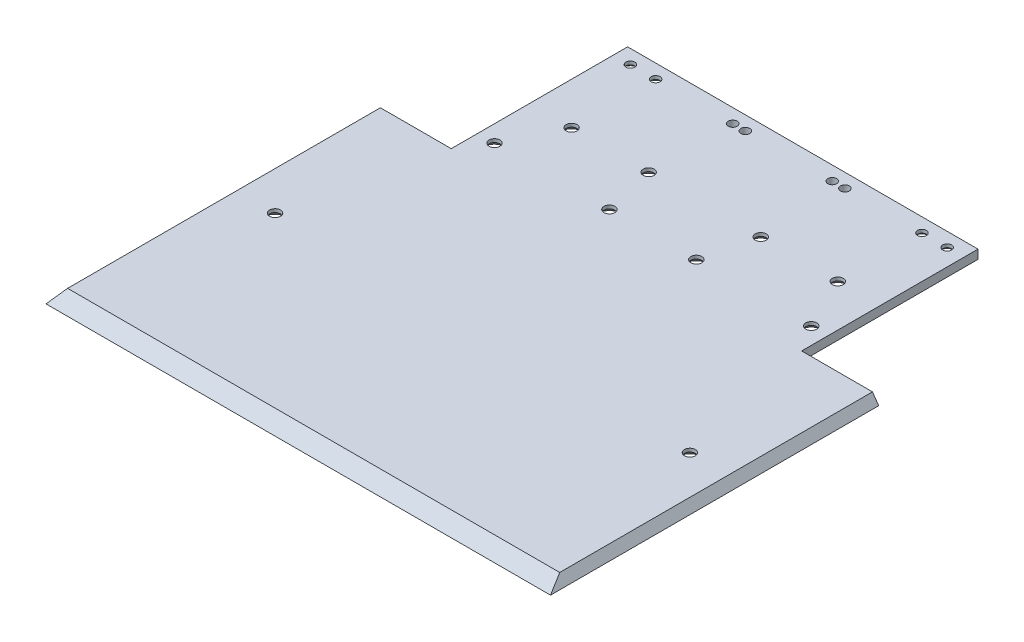
SolidWorks part; units mm, degrees
ref_plane "Alzado" through (0, 0, 0) normal (0, 0, 1) x (1, 0, 0)
ref_plane "Planta" through (0, 0, 0) normal (0, 1, 0) x (1, 0, 0)
ref_plane "Vista lateral" through (0, 0, 0) normal (1, 0, 0) x (0, 0, -1)
sketch "Croquis1" plane through (0, 0, 0) normal (0, 1, 0) x (1, 0, 0)
  line L0 (-62.5, 90) -> (-62.5, 27.08)
  line L1 (90, -90) -> (-90, -90)
  line L2 (90, -90) -> (90, 27.08)
  line L3 (62.5, 90) -> (-62.5, 90)
  line L4 (-90, -90) -> (-90, 27.08)
  line L5 (90, -90) -> (-62.5, 62.5) construction
  line L6 (62.5, 62.5) -> (-90, -90) construction
  line L7 (-62.5, 27.08) -> (-90, 27.08)
  line L8 (0, 90) -> (0, -90) construction
  line L9 (62.5, 27.08) -> (90, 27.08)
  line L10 (62.5, 90) -> (62.5, 27.08)
  point P0 (0, 0)
  dimension "D1" = 125
  dimension "D2" = 180
  dimension "D3" = 27.5
  dimension "D4" = 62.92
  dimension "D5" = 27.5
extrude "Saliente-Extruir1" add sketch "Croquis1" along normal blind 3.17
sketch "Croquis2" plane through (-90, 0, 0) normal (-1, 0, 0) x (0, 0, 1)
  line L0 (90, 0) -> (84.5094, 3.17)
  line L1 (-27.08, 3.17) -> (90, 3.17) construction
  line L2 (84.5094, 3.17) -> (90, 3.17)
  line L3 (90, 3.17) -> (90, 0)
  dimension "D1" = 60
extrude "Cortar-Extruir1" cut sketch "Croquis2" against normal up to next
sketch "Croquis16" plane through (0, 0, -27.08) normal (0, 0, -1) x (-1, 0, 0)
  line L0 (90, 3.17) -> (90, 0)
  line L1 (90, 0) -> (87.7803, 3.17)
  line L2 (62.5, 3.17) -> (90, 3.17) construction
  line L3 (87.7803, 3.17) -> (90, 3.17)
  dimension "D1" = 35
extrude "Cortar-Extruir7" cut sketch "Croquis16" against normal up to next
mirror "Simetría4" about plane through (0, 0, 0) normal (1, 0, 0) of "Cortar-Extruir7"
sketch "Croquis3" plane through (0, 3.17, 0) normal (0, 1, 0) x (1, 0, 0)
  circle A0 centre (74, -24.2793) radius 1.585
extrude "Cortar-Extruir2" cut sketch "Croquis3" against normal up to next (3.17 mm away)
mirror "Simetría1" about plane through (0, 0, 0) normal (1, 0, 0) of "Cortar-Extruir2"
sketch "Croquis4" plane through (0, 3.17, 0) normal (0, 1, 0) x (1, 0, 0)
  circle A0 centre (-56.5, 36.5006) radius 1.585
  circle A1 centre (-15.5, 36.5006) radius 1.585
  circle A2 centre (-15.5, 85.0006) radius 1.585
  circle A3 centre (-56.5, 85.0006) radius 1.585
extrude "Cortar-Extruir3" cut sketch "Croquis4" against normal up to next
sketch "Croquis6" plane through (0, 3.17, 0) normal (0, 1, 0) x (1, 0, 0)
  circle A0 centre (56.5, 85.0006) radius 1.585
  circle A1 centre (15.5, 85.0006) radius 1.585
  circle A2 centre (15.5, 36.5006) radius 1.585
  circle A3 centre (56.5, 36.5006) radius 1.585
extrude "Cortar-Extruir4" cut sketch "Croquis6" against normal up to next
sketch "Croquis7" plane through (0, 3.17, 0) normal (0, 1, 0) x (1, 0, 0)
  circle A0 centre (-20, 85.0006) radius 1.585
  circle A1 centre (-47.5, 85.0006) radius 1.585
  circle A2 centre (-47.5, 55.0006) radius 1.585
  circle A3 centre (-20, 55.0006) radius 1.585
extrude "Cortar-Extruir5" cut sketch "Croquis7" against normal up to next (3.17 mm away)
mirror "Simetría2" about plane through (0, 0, 0) normal (1, 0, 0) of "Cortar-Extruir5"
sketch "Croquis15" plane through (0, 0, 0) normal (0, -1, 0) x (-1, 0, 0)
  circle A0 centre (20, 55.0006) radius 4
  circle A1 centre (15.5, 36.5006) radius 4
  circle A2 centre (56.5, 36.5006) radius 4
  circle A3 centre (47.5, 55.0006) radius 4
  circle A4 centre (56.5, 85.0006) radius 4
  circle A5 centre (47.5, 85.0006) radius 4
  circle A8 centre (74, -24.2793) radius 4
  dimension "D1" = 8
  dimension "D3" = 8
  dimension "D4" = 8
  dimension "D5" = 8
  dimension "D6" = 8
  dimension "D7" = 8
  dimension "D8" = 8
extrude "Cortar-Extruir6" cut sketch "Croquis15" against normal blind 2 draft 50.5
mirror "Simetría3" about plane through (0, 0, 0) normal (1, 0, 0) of "Cortar-Extruir6"
sketch "Croquis13" plane through (0, 0, 0) normal (0, -1, 0) x (-1, 0, 0)
  point P0 (-74, -24.2793)
  point P3 (-56.5, 36.5006)
  point P6 (-47.5, 55.0006)
  point P9 (-20, 55.0006)
  point P12 (-15.5, 36.5006)
  point P15 (15.5, 36.5006)
  point P18 (20, 55.0006)
  point P21 (47.5, 55.0006)
  point P24 (56.5, 36.5006)
  point P27 (74, -24.2793)
hole_wizard "Avellanado para tornillo con cabeza avellanada en cruz de M3.51" positions "Croquis13" profile "Croquis14" countersink size "M3.5" standard "AS" end condition through all
sketch "Croquis14" plane through (74, 0, 24.2793) normal (1, 0, 0) x (0, 0, -1)
  line L0 (0, 0) -> (0, 3.17)
  line L1 (0, 3.17) -> (1.95, 3.17)
  line L2 (1.95, 3.17) -> (1.95, 1.9797)
  line L3 (1.95, 1.9797) -> (4, 0)
  line L5 (4, 0) -> (0, 0)
  line L6 (-1.95, 1.9797) -> (-4, 0) construction
  line L11 (0, -6.35) -> (0, 107.95) construction
  dimension "Diámetro de taladro hasta el siguiente" = 3.9
  dimension "Profundidad de taladro hasta el siguiente" = 3.17
  dimension "Diámetro de avellanado cercano" = 8
  dimension "Ángulo de avellanado cercano" = 92
